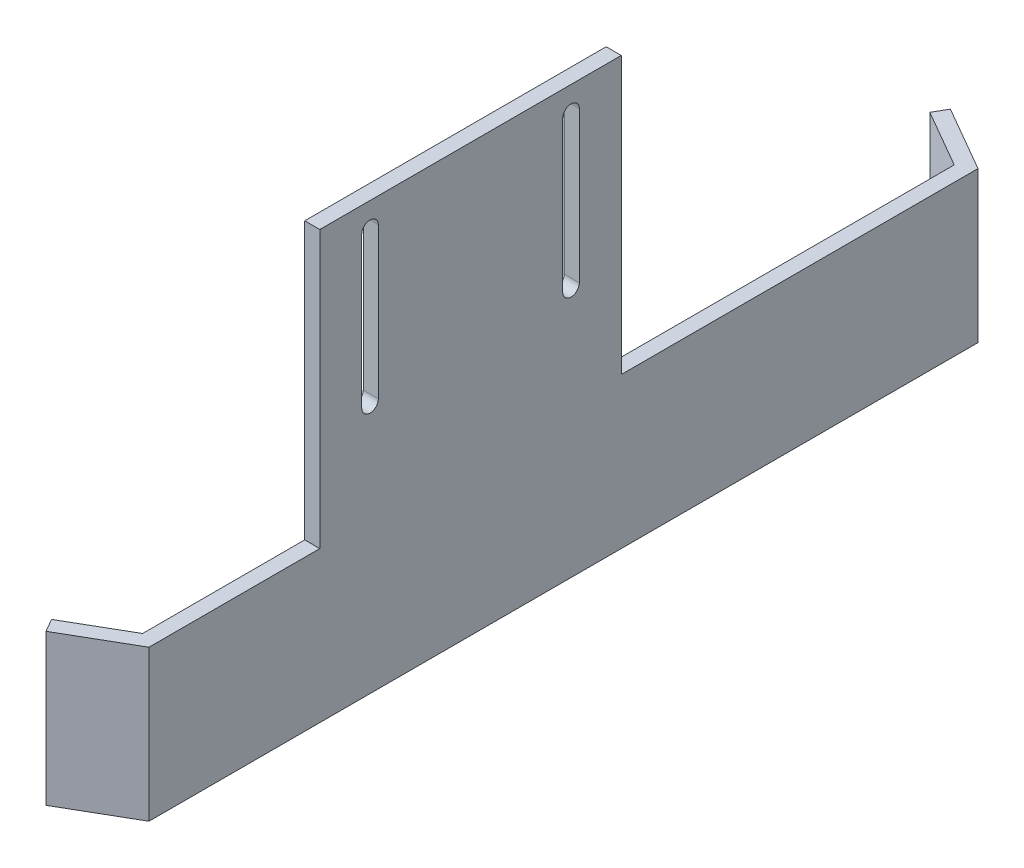
SolidWorks part; units mm, degrees
other "Marquage1"
sketch "Esquisse10" plane through (85, 10, -107) normal (0.2519, 0.9677, -0.0136) x (0.8563, -0.2294, -0.4627)
sketch "Esquisse11" plane through (85, 10, -107) normal (0.2519, 0.9677, -0.0136) x (0.8563, -0.2294, -0.4627)
sketch "Esquisse15" plane through (85, 30, -107) normal (0.2519, 0.9677, -0.0136) x (0.8563, -0.2294, -0.4627)
ref_plane "Plan de face" through (0, 0, 0) normal (0, 0, 1) x (1, 0, 0)
ref_plane "Plan de dessus" through (0, 0, 0) normal (0, 1, 0) x (1, 0, 0)
ref_plane "Plan de droite" through (0, 0, 0) normal (1, 0, 0) x (0, 0, -1)
sketch "Esquisse1" plane through (0, 0, 0) normal (0, 0, 1) x (1, 0, 0)
  line L0 (5, 10) -> (5, 0) construction
  line L1 (0, 0) -> (85, 0)
  line L2 (0, 0) -> (0, 10)
  line L3 (0, 10) -> (85, 10)
  line L4 (85, 0) -> (85, 10)
  circle A0 centre (5, 5) radius 1
  point P10 (5, 5)
  dimension "D1" = 2
  dimension "D2" = 10
  dimension "D3" = 80
  dimension "D4" = 10
extrude "Boss.-Extru.1" add sketch "Esquisse1" along normal blind 3
sketch "Esquisse2" plane through (85, 0, 0) normal (1, 0, 0) x (0, 0, -1)
  line L0 (-3, 10) -> (0, 10) construction
  line L1 (-65.5, 10) -> (99.5, 10)
  line L2 (-65.5, 10) -> (-65.5, -55)
  line L3 (-65.5, -55) -> (99.5, -55)
  line L4 (99.5, 10) -> (99.5, -55)
  line L5 (-133, -115.6313) -> (-133, -112.6982) construction
  dimension "D1" = 65
  dimension "D2" = 165
  dimension "D3" = 67.5
extrude "Boss.-Extru.2" add sketch "Esquisse2" against normal blind 3
sketch "Esquisse3" plane through (85, 0, 0) normal (1, 0, 0) x (0, 0, -1)
  line L0 (-65.5, -55) -> (99.5, -55) construction
  line L5 (-65.5, 10) -> (99.5, 10) construction
  line L8 (-65.5, 10) -> (-65.5, -55) construction
  line L9 (-31.5, 10) -> (-65.5, 10)
  line L10 (-31.5, 10) -> (-31.5, -25)
  line L11 (-31.5, -25) -> (-65.5, -25)
  line L12 (-65.5, 10) -> (-65.5, -25)
  line L13 (99.5, 10) -> (28.5, 10)
  line L14 (99.5, 10) -> (99.5, -25)
  line L15 (99.5, -25) -> (28.5, -25)
  line L16 (28.5, 10) -> (28.5, -25)
  dimension "D1" = 71
  dimension "D2" = 34
  dimension "D3" = 30
  dimension "D4" = 30
extrude "Enlèv. mat.-Extru.1" cut sketch "Esquisse3" against normal up to next
sketch "Esquisse5" plane through (0, 10, 0) normal (0, 1, 0) x (1, 0, 0)
  line L0 (63.7077, 0) -> (82, 28.5)
  line L1 (82, 0) -> (0, 0) construction
  line L3 (82, 28.5) -> (82, 0)
  line L4 (82, 0) -> (63.7077, 0)
  line L5 (63.7077, -3) -> (82, -3)
  line L6 (82, -3) -> (0, -3) construction
  line L7 (82, -3) -> (82, -31.5)
  line L9 (82, -31.5) -> (63.7077, -3)
  line L10 (82, -3) -> (82, -31.5) construction
  line L11 (82, -3) -> (82, -31.5) construction
extrude "Boss.-Extru.3" add sketch "Esquisse5" against normal blind 10
sketch "Esquisse7" plane through (0, -55, 0) normal (0, -1, 0) x (1, 0, 0)
  line L0 (85, 65.5) -> (72.0096, 73)
  line L1 (72.0096, 73) -> (70.5096, 70.4019)
  line L2 (70.5096, 70.4019) -> (82, 63.7679)
  line L3 (82, 65.5) -> (82, -99.5) construction
  line L4 (85, 65.5) -> (85, -99.5) construction
  line L5 (85, -17) -> (77.9383, -17) construction
  line L6 (82, 63.7679) -> (85, 65.5)
  line L7 (70.5096, -104.4019) -> (82, -97.7679)
  line L8 (72.0096, -107) -> (70.5096, -104.4019)
  line L9 (85, -99.5) -> (72.0096, -107)
  line L10 (82, -97.7679) -> (85, -99.5)
  dimension "D1" = 3
  dimension "D2" = 120
  dimension "D3" = 15
extrude "Boss.-Extru.5" add sketch "Esquisse7" against normal blind 30
sketch "Esquisse8" plane through (85, 0, 0) normal (1, 0, 0) x (0, 0, -1)
  line L0 (-31.5, 5) -> (28.5, 5) construction
  line L1 (-31.5, -25) -> (-31.5, 10) construction
  line L3 (28.5, 10) -> (28.5, -25) construction
  line L4 (-31.5, 10) -> (28.5, 10) construction
  circle A0 centre (-21.5, 5) radius 1.65
  circle A1 centre (18.5, 5) radius 1.65
  dimension "D1" = 3.3
  dimension "D2" = 3.3
  dimension "D3" = 10
  dimension "D4" = 10
  dimension "D5" = 5
extrude "Enlèv. mat.-Extru.2" cut sketch "Esquisse8" against normal up to next and the other way through all
ref_plane "Plan1" through (72, 0, 0) normal (-1, 0, 0) x (0, 0, 1)
sketch "Esquisse9" plane through (72, 0, 0) normal (-1, 0, 0) x (0, 0, 1)
  line L6 (-16.8546, 7.85) -> (-20.1454, 7.85)
  line L7 (-20.1454, 7.85) -> (-21.7909, 5)
  line L8 (-21.7909, 5) -> (-20.1454, 2.15)
  line L9 (-20.1454, 2.15) -> (-16.8546, 2.15)
  line L10 (-16.8546, 2.15) -> (-15.2091, 5)
  line L11 (-15.2091, 5) -> (-16.8546, 7.85)
  line L12 (-21.7909, 5) -> (-15.2091, 5) construction
  line L13 (23.1454, 7.85) -> (19.8546, 7.85)
  line L14 (19.8546, 7.85) -> (18.2091, 5)
  line L15 (18.2091, 5) -> (19.8546, 2.15)
  line L16 (19.8546, 2.15) -> (23.1454, 2.15)
  line L17 (23.1454, 2.15) -> (24.7909, 5)
  line L18 (24.7909, 5) -> (23.1454, 7.85)
  line L19 (18.2091, 5) -> (24.7909, 5) construction
  point P0 (-18.5, 5)
  point P4 (-18.5, 2.15)
  point P8 (-18.5, 5)
  point P9 (-18.5, 5)
  point P10 (-18.5, 5)
  point P11 (21.5, 5)
  point P13 (21.5, 5)
  point P18 (21.5, 2.15)
  point P22 (21.5, 5)
  point P23 (21.5, 5)
  dimension "D1" = 5.7
  dimension "D2" = 120
  dimension "D3" = 5.7
  dimension "D4" = 5.7
  dimension "D5" = 120
  dimension "D6" = 5.7
extrude "Enlèv. mat.-Extru.3" cut sketch "Esquisse9" against normal blind 8
sketch "Esquisse12" plane through (0, 10, 0) normal (0, 1, 0) x (1, 0, 0)
  line L0 (82, 97.7679) -> (82, 28.5) construction
  line L1 (82, 45.1647) -> (-13.2269, 45.1647)
  line L2 (82, 45.1647) -> (82, -40.6849)
  line L3 (82, -40.6849) -> (-13.2269, -40.6849)
  line L4 (-13.2269, 45.1647) -> (-13.2269, -40.6849)
extrude "Enlèv. mat.-Extru.4" cut sketch "Esquisse12" against normal through all
sketch "Esquisse13" plane through (82, 0, 0) normal (-1, 0, 0) x (0, 0, 1)
  line L1 (-28.5, 10) -> (31.5, 10)
  line L2 (-28.5, 10) -> (-28.5, 30)
  line L3 (-28.5, 30) -> (31.5, 30)
  line L4 (31.5, 10) -> (31.5, 30)
  dimension "D1" = 20
extrude "Boss.-Extru.6" add sketch "Esquisse13" against normal blind 3
sketch "Esquisse14" plane through (82, 0, 0) normal (-1, 0, 0) x (0, 0, 1)
  line L0 (-18.5, -5) -> (-18.5, 25) construction
  line L1 (-20.15, -5) -> (-20.15, 25)
  line L2 (-16.85, -5) -> (-16.85, 25)
  line L3 (21.5, -5) -> (21.5, 25) construction
  line L4 (19.85, -5) -> (19.85, 25)
  line L5 (23.15, -5) -> (23.15, 25)
  line L6 (-28.5, -25) -> (-28.5, 30) construction
  line L7 (31.5, 30) -> (31.5, -25) construction
  line L8 (31.5, 30) -> (-28.5, 30) construction
  arc A0 (-20.15, -5) -> (-16.85, -5) centre (-18.5, -5) ccw
  arc A1 (-16.85, 25) -> (-20.15, 25) centre (-18.5, 25) ccw
  arc A2 (19.85, -5) -> (23.15, -5) centre (21.5, -5) ccw
  arc A3 (23.15, 25) -> (19.85, 25) centre (21.5, 25) ccw
  point P2 (-18.5, 10)
  point P7 (21.5, 10)
  dimension "D1" = 3.3
  dimension "D2" = 3.3
  dimension "D3" = 30
  dimension "D4" = 30
  dimension "D5" = 10
  dimension "D6" = 10
  dimension "D7" = 5
  dimension "D8" = 5
extrude "Enlèv. mat.-Extru.5" cut sketch "Esquisse14" against normal blind 3
